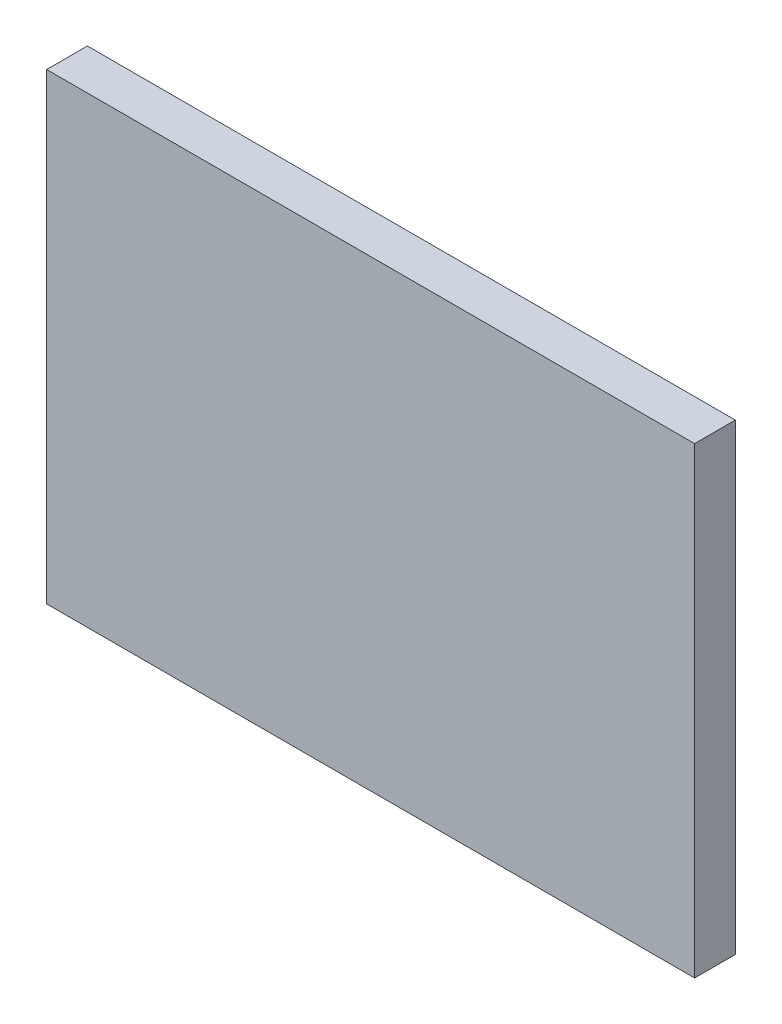
SolidWorks part; units mm, degrees
ref_plane "前视基准面" through (0, 0, 0) normal (0, 0, 1) x (1, 0, 0)
ref_plane "上视基准面" through (0, 0, 0) normal (0, 1, 0) x (1, 0, 0)
ref_plane "右视基准面" through (0, 0, 0) normal (1, 0, 0) x (0, 0, -1)
sketch "草图1" plane through (0, 0, 0) normal (0, 0, 1) x (1, 0, 0)
  line L1 (-8.75, -6.25) -> (8.75, -6.25)
  line L2 (-8.75, -6.25) -> (-8.75, 6.25)
  line L3 (-8.75, 6.25) -> (8.75, 6.25)
  line L4 (8.75, -6.25) -> (8.75, 6.25)
  line L5 (-8.75, -6.25) -> (8.75, 6.25) construction
  line L6 (-8.75, 6.25) -> (8.75, -6.25) construction
  circle A0 centre (0, 0) radius 8.75 construction
  dimension "D1" = 17.5
  dimension "D2" = 12.5
  dimension "D3" = 17.5
extrude "凸台-拉伸1" add sketch "草图1" along normal blind 1.1
